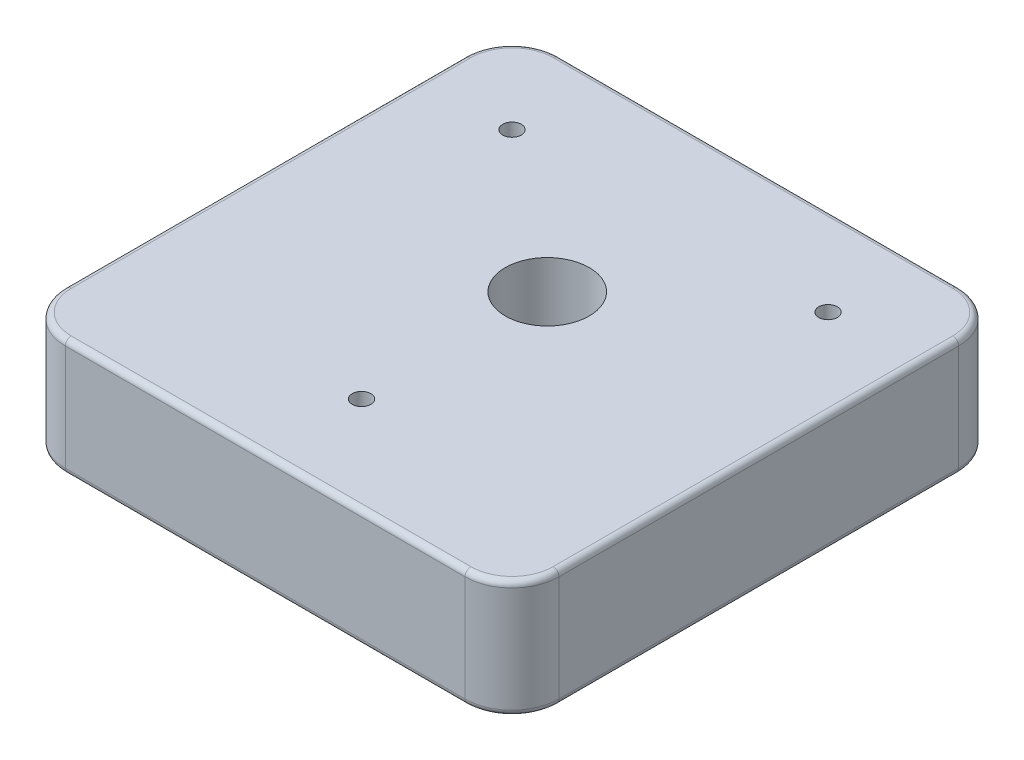
SolidWorks part; units mm, degrees
ref_plane "Front" through (0, 0, 0) normal (0, 0, 1) x (1, 0, 0)
ref_plane "Top" through (0, 0, 0) normal (0, 1, 0) x (1, 0, 0)
ref_plane "Right" through (0, 0, 0) normal (1, 0, 0) x (0, 0, -1)
sketch "Sketch1" plane through (0, 0, 0) normal (0, 1, 0) x (1, 0, 0)
  line L0 (21, 21) -> (-21, -21) construction
  line L1 (-21, -21) -> (21, -21)
  line L2 (-21, -21) -> (-21, 21)
  line L3 (-21, 21) -> (21, 21)
  line L4 (21, -21) -> (21, 21)
  point P4 (0, 0)
  dimension "D1" = 42
extrude "Extrude1" add sketch "Sketch1" along normal blind 10
sketch "Sketch2" plane through (0, 0, 0) normal (0, -1, 0) x (1, 0, 0)
  line L4 (0, 0) -> (-15.3382, 0) construction
  line L6 (15, -15) -> (-15, -15) construction
  line L7 (0, -15) -> (0, 15) construction
  circle A0 centre (-15, -15) radius 3.1813
  circle A1 centre (15, -15) radius 3.1813
  circle A2 centre (0, 15) radius 3.1813
  point P0 (0, 0)
  point P1 (0, -3)
  point P11 (0, -15)
  point P14 (15, -15)
  point P20 (0, 15)
  dimension "D2" = 6.3627
  dimension "D1" = 30
  dimension "D3" = 30
  dimension "D4" = 12
extrude "Extrude2" cut sketch "Sketch2" against normal blind 3.1877
hole_wizard "1/4 Clearance Hole1" positions "3DSketch2" profile "Sketch4" hole size "1/4" standard "Ansi Inch" end condition through all
sketch3d "3DSketch2"
  point P0 (0, 0, -3)
sketch "Sketch4" plane through (0, 0, -3) normal (1, 0, 0) x (0, 0, -1)
  line L0 (0, 0) -> (0, 10)
  line L1 (0, 10) -> (3.5712, 10)
  line L2 (3.5712, 10) -> (3.5712, 0)
  line L5 (3.5712, 0) -> (0, 0)
  line L11 (0, -6.35) -> (0, 107.95) construction
  dimension "Thru Hole Dia." = 7.1425
  dimension "Thru Hole Depth" = 10
fillet "Fillet1" radius 4 4 edges at (21, 5, 21) (-21, 5, 21) (-21, 5, -21) (21, 5, -21)
fillet "Fillet2" radius 1.5875 3 edges at (0, 3.1877, 11.8186) (-15, 3.1877, -18.1813) (15, 3.1877, -18.1813)
sketch "Sketch5" plane through (0, 0, 0) normal (0, -1, 0) x (1, 0, 0)
  line L0 (0, 0) -> (-15, -15) construction
  line L1 (0, 0) -> (15, -15) construction
  line L2 (0, 0) -> (0, 15) construction
  point P1 (-13.4444, -13.4444)
  point P3 (0, 12.8)
  point P10 (13.4444, -13.4444)
  dimension "D1" = 2.2
  dimension "D2" = 2.2
hole_wizard "1/16 (0.0625) Diameter Hole1" positions "3DSketch3" profile "Sketch6" hole size "1/16" standard "Ansi Inch" end condition through all
sketch3d "3DSketch3"
  point P0 (0, 0, 12.8)
  point P3 (-13.4444, 0, -13.4444)
  point P6 (13.4444, 0, -13.4444)
sketch "Sketch6" plane through (0, 0, 12.8) normal (1, 0, 0) x (0, 0, -1)
  line L0 (0, 0) -> (0, 10)
  line L1 (0, 10) -> (0.7937, 10)
  line L2 (0.7937, 10) -> (0.7937, 0)
  line L5 (0.7937, 0) -> (0, 0)
  line L11 (0, -6.35) -> (0, 107.95) construction
  dimension "Thru Hole Dia." = 1.5875
  dimension "Thru Hole Depth" = 10
fillet "Fillet3" radius 0.5 16 edges at (19.8284, 0, 19.8284) (0, 0, 21) (-19.8284, 0, 19.8284) (-21, 0, 0) (-19.8284, 0, -19.8284) (0, 0, -21) (19.8284, 0, -19.8284) (19.8284, 10, 19.8284) (0, 10, 21) (-19.8284, 10, 19.8284) (-21, 10, 0) (-19.8284, 10, -19.8284) (0, 10, -21) (19.8284, 10, -19.8284) (21, 0, 0) (21, 10, 0)
